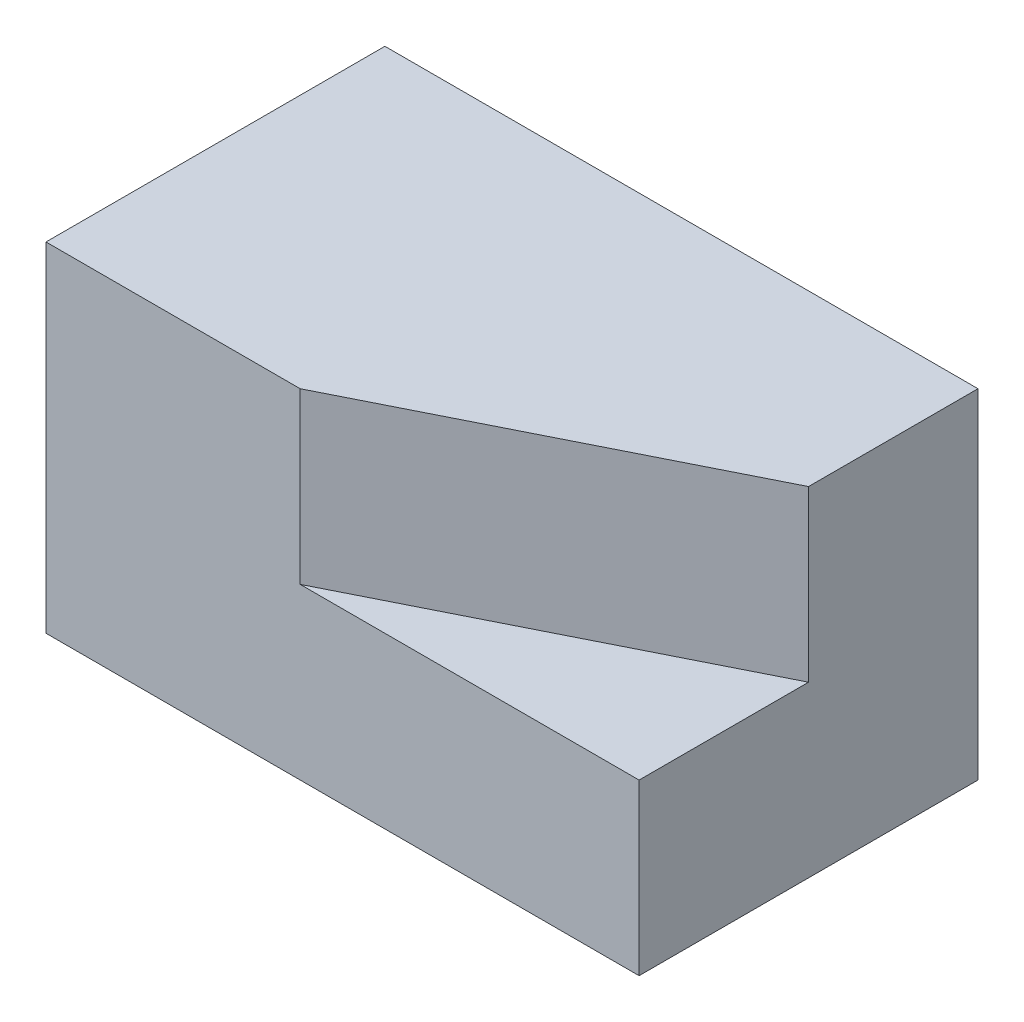
SolidWorks part; units mm, degrees
ref_plane "Front Plane" through (0, 0, 0) normal (0, 0, 1) x (1, 0, 0)
ref_plane "Top Plane" through (0, 0, 0) normal (0, 1, 0) x (1, 0, 0)
ref_plane "Right Plane" through (0, 0, 0) normal (1, 0, 0) x (0, 0, -1)
sketch "Sketch1" plane through (0, 0, 0) normal (0, 0, 1) x (1, 0, 0)
  line L1 (0, 0) -> (177.8, 0)
  line L2 (0, 0) -> (0, 50.8)
  line L3 (0, 50.8) -> (177.8, 50.8)
  line L4 (177.8, 0) -> (177.8, 50.8)
extrude "Boss-Extrude2" add sketch "Sketch1" against normal blind 101.6
sketch "Sketch4" plane through (0, 50.8, 0) normal (0, 1, 0) x (1, 0, 0)
  line L1 (177.8, 101.6) -> (177.8, 0) construction
  line L2 (76.2, 50.8) -> (76.2, 0)
  line L3 (177.8, 0) -> (0, 0) construction
  line L4 (76.2, 0) -> (177.8, 50.8)
  line L6 (177.8, 101.6) -> (0, 101.6) construction
  line L8 (177.3958, 101.6) -> (177.3958, 50.8)
  line L9 (177.3958, 50.8) -> (76.2, 50.8)
  line L12 (0, 0) -> (177.8, 0)
  line L13 (177.8, 0) -> (177.8, 101.6)
  line L14 (177.8, 101.6) -> (0, 101.6)
  line L15 (0, 101.6) -> (0, 0)
  line L17 (177.8, 50.8) -> (177.8, 101.6)
  line L18 (177.8, 101.6) -> (177.3958, 101.6)
  dimension "D1" = 0
sketch "Sketch5" plane through (0, 0, 0) normal (1, 0, 0) x (0, 0, -1)
  line L0 (101.6, 50.8) -> (101.6, 101.6)
  line L1 (101.6, 101.6) -> (0, 101.6)
  line L2 (0, 101.6) -> (0, 50.8)
  line L8 (0, 50.8) -> (0, 0)
  line L9 (101.6, 50.8) -> (0, 50.8)
  line L10 (101.6, 0) -> (101.6, 50.8)
  line L11 (0, 0) -> (101.6, 0)
  line L13 (101.6, 50.8) -> (0, 50.8)
  dimension "D1" = 0
extrude "Boss-Extrude3" add sketch "Sketch5" along normal blind 76.2
extrude "Boss-Extrude4" add sketch "Sketch4" along normal blind 50.8
ref_plane "Plane1" through (76.2, 101.6, -101.6) normal (0, 0, 1) x (1, 0, 0)
sketch "Sketch6" plane through (76.2, 101.6, -101.6) normal (0, 0, 1) x (1, 0, 0)
  line L1 (0, -50.8) -> (101.6, -50.8)
  line L2 (0, -50.8) -> (0, 0)
  line L3 (0, 0) -> (101.6, 0)
  line L4 (101.6, -50.8) -> (101.6, 0)
extrude "Boss-Extrude5" add sketch "Sketch6" along normal up to next contours L3 L4 L1 L2
sketch "Sketch7" plane through (0, 0, 0) normal (1, 0, 0) x (0, 0, -1)
  line L0 (50.8, 101.6) -> (50.8, 50.8)
  line L1 (101.6, 101.6) -> (0, 101.6) construction
  line L2 (50.8, 50.8) -> (0, 50.8)
  line L3 (0, 101.6) -> (0, 0) construction
  line L4 (0, 50.8) -> (50.8, 101.6)
  dimension "D1" = 50.8
